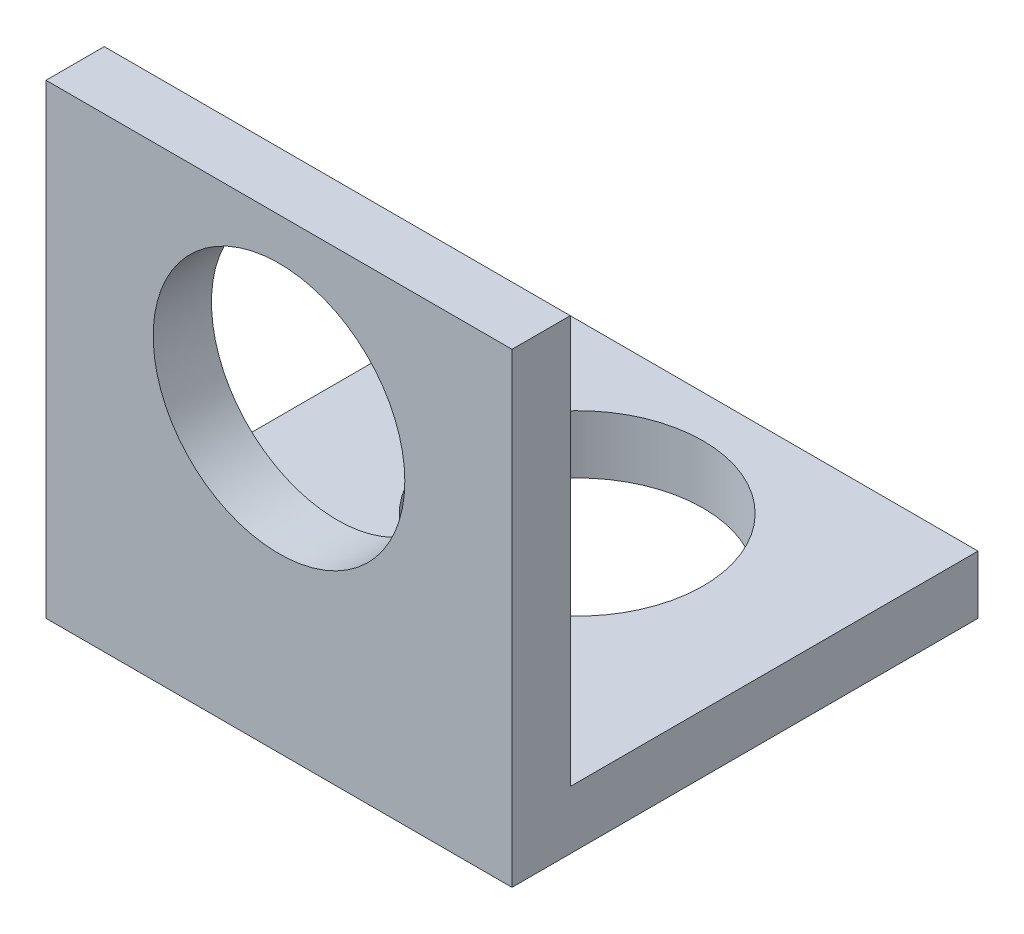
SolidWorks part; units mm, degrees
material "5052-H32"
ref_plane "Front Plane" through (0, 0, 0) normal (0, 0, 1) x (1, 0, 0)
ref_plane "Top Plane" through (0, 0, 0) normal (0, 1, 0) x (1, 0, 0)
ref_plane "Right Plane" through (0, 0, 0) normal (1, 0, 0) x (0, 0, -1)
sketch "Sketch1" plane through (0, 0, 0) normal (1, 0, 0) x (0, 0, -1)
  line L0 (0, 0) -> (0, 12.7)
  line L1 (0, 0) -> (12.7, 0)
  line L2 (1.5875, 1.5875) -> (12.7, 1.5875)
  line L3 (1.5875, 1.5875) -> (1.5875, 12.7)
  line L4 (0, 12.7) -> (1.5875, 12.7)
  line L5 (12.7, 1.5875) -> (12.7, 0)
  dimension "D1" = 1.5875
  dimension "D2" = 12.7
extrude "Boss-Extrude1" add sketch "Sketch1" along normal blind 12.7
sketch "Sketch2" plane through (0, 0, 0) normal (0, 0, 1) x (1, 0, 0)
  line L0 (12.7, 12.7) -> (0, 12.7) construction
  line L1 (12.7, 12.7) -> (12.7, 0) construction
  circle A0 centre (6.35, 8.128) radius 3.429
  dimension "D1" = 4.572
  dimension "D3" = 6.858
  dimension "D2" = 6.35
extrude "Cut-Extrude1" cut sketch "Sketch2" against normal through all
sketch "Sketch3" plane through (0, 0, 0) normal (0, -1, 0) x (1, 0, 0)
  line L0 (12.7, -12.7) -> (0, -12.7) construction
  line L1 (0, 0) -> (0, -12.7) construction
  circle A0 centre (6.35, -8.128) radius 3.429
  dimension "D1" = 6.858
  dimension "D2" = 4.572
  dimension "D3" = 6.35
extrude "Cut-Extrude2" cut sketch "Sketch3" against normal through all
